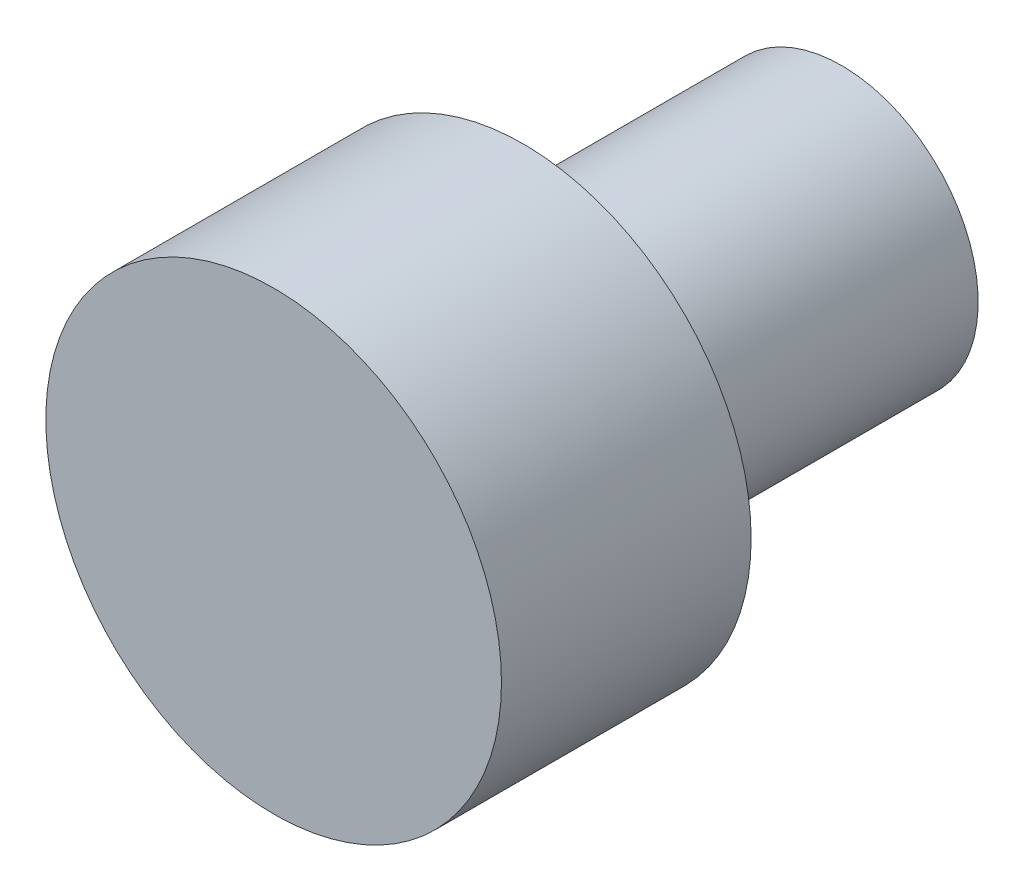
SolidWorks part; units mm, degrees
material "Cast Stainless Steel"
ref_plane "Front Plane" through (0, 0, 0) normal (0, 0, 1) x (1, 0, 0)
ref_plane "Top Plane" through (0, 0, 0) normal (0, 1, 0) x (1, 0, 0)
ref_plane "Right Plane" through (0, 0, 0) normal (1, 0, 0) x (0, 0, -1)
sketch "Sketch1" plane through (0, 0, 0) normal (0, 0, 1) x (1, 0, 0)
  circle A0 centre (0, 0) radius 9.271
  dimension "D1" = 18.542
extrude "Boss-Extrude1" add sketch "Sketch1" along normal blind 10.16
sketch "Sketch2" plane through (0, 0, 0) normal (0, 0, -1) x (-1, 0, 0)
  circle A0 centre (0, 0) radius 5.5562
  dimension "D1" = 11.1125
extrude "Boss-Extrude2" add sketch "Sketch2" along normal blind 12.954
